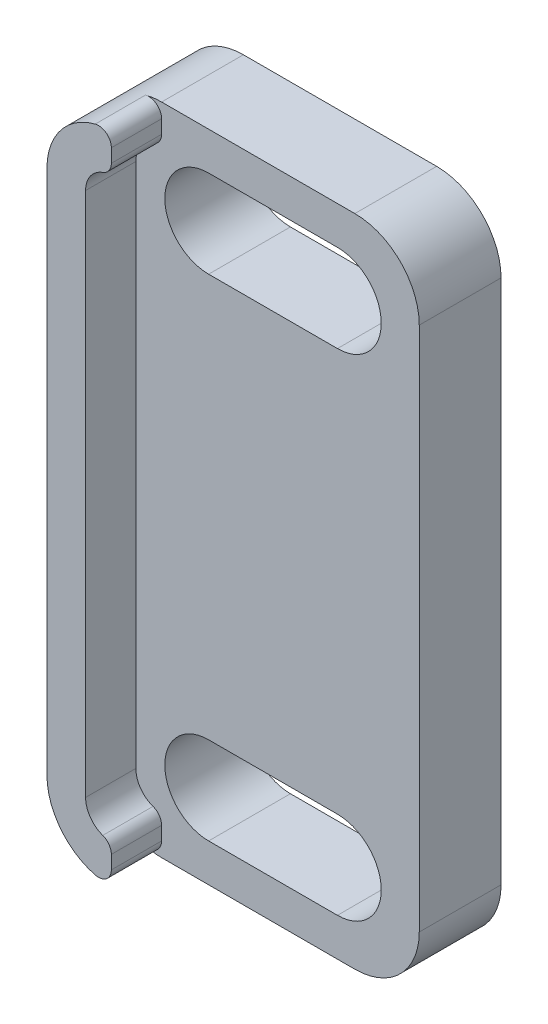
SolidWorks part; units mm, degrees
ref_plane "Front Plane" through (0, 0, 0) normal (0, 0, 1) x (1, 0, 0)
ref_plane "Top Plane" through (0, 0, 0) normal (0, 1, 0) x (1, 0, 0)
ref_plane "Right Plane" through (0, 0, 0) normal (1, 0, 0) x (0, 0, -1)
sketch "Sketch1" plane through (0, 0, 0) normal (0, 0, 1) x (1, 0, 0)
  line L0 (4.325, 3.175) -> (9.325, 3.175) construction
  line L1 (0, 0) -> (12.5, 0)
  line L2 (0, 0) -> (0, 25.4)
  line L3 (0, 25.4) -> (12.5, 25.4)
  line L4 (12.5, 0) -> (12.5, 25.4)
  line L5 (0, 0) -> (12.5, 25.4) construction
  line L6 (0, 25.4) -> (12.5, 0) construction
  line L7 (4.325, 4.875) -> (9.325, 4.875)
  line L8 (4.325, 1.475) -> (9.325, 1.475)
  line L9 (4.325, 22.225) -> (9.325, 22.225) construction
  line L10 (4.325, 23.925) -> (9.325, 23.925)
  line L11 (4.325, 20.525) -> (9.325, 20.525)
  arc A2 (4.325, 4.875) -> (4.325, 1.475) centre (4.325, 3.175) ccw
  arc A3 (9.325, 1.475) -> (9.325, 4.875) centre (9.325, 3.175) ccw
  arc A4 (4.325, 23.925) -> (4.325, 20.525) centre (4.325, 22.225) ccw
  arc A5 (9.325, 20.525) -> (9.325, 23.925) centre (9.325, 22.225) ccw
  point P4 (6.25, 12.7)
  point P10 (6.825, 3.175)
  point P17 (6.825, 22.225)
  dimension "D1" = 12.5
  dimension "D2" = 25.4
  dimension "D7" = 19.05
  dimension "D8" = 3.4
  dimension "D9" = 3.4
  dimension "D10" = 9.525
  dimension "6" = 5
  dimension "D12" = 3.175
extrude "Boss-Extrude1" add sketch "Sketch1" along normal blind 3.175
fillet "Fillet1" radius 2.5 4 edges at (0, 0, 1.5875) (12.5, 0, 1.5875) (12.5, 25.4, 1.5875) (0, 25.4, 1.5875)
sketch "Sketch2" plane through (0, 0, 3.175) normal (0, 0, 1) x (1, 0, 0)
  line L0 (0, 22.9) -> (0, 2.5) construction
  line L1 (0, 22.9) -> (0, 2.5)
  line L2 (1.5, 22.9) -> (1.5, 2.5)
  line L3 (2.5, 23.9) -> (2.5, 25.4)
  line L4 (2.5, 1.5) -> (2.5, 0)
  arc A0 (0, 2.5) -> (2.5, 0) centre (2.5, 2.5) ccw construction
  arc A1 (2.5, 25.4) -> (0, 22.9) centre (2.5, 22.9) ccw construction
  arc A2 (0, 2.5) -> (2.5, 0) centre (2.5, 2.5) ccw
  arc A3 (2.5, 25.4) -> (0, 22.9) centre (2.5, 22.9) ccw
  arc A4 (2.5, 23.9) -> (1.5, 22.9) centre (2.5, 22.9) ccw
  arc A5 (1.5, 2.5) -> (2.5, 1.5) centre (2.5, 2.5) ccw
  dimension "D1" = 1.5
extrude "Boss-Extrude2" add sketch "Sketch2" along normal blind 1.95 contours L1 A2 L4 A5 L2 A4 L3 A3
fillet "Fillet2" radius 0.5 4 edges at (2.5, 0, 4.15) (2.5, 1.5, 4.15) (2.5, 23.9, 4.15) (2.5, 25.4, 4.15)
ref_plane "Plane1" through (0, 0, 0) normal (0, 0, -1) x (-1, 0, 0)
